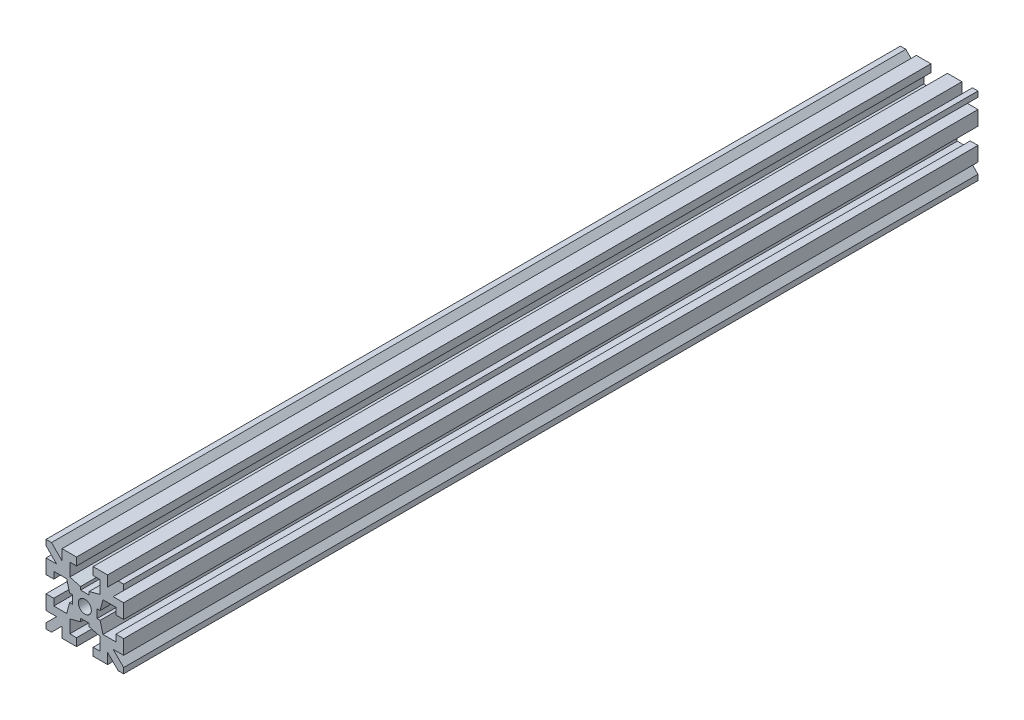
SolidWorks part; units mm, degrees
material "3.0205 (EN-AW 1200)"
ref_plane "Plano frontal" through (0, 0, 0) normal (0, 0, 1) x (1, 0, 0)
ref_plane "Plano superior" through (0, 0, 0) normal (0, 1, 0) x (1, 0, 0)
ref_plane "Plano direito" through (0, 0, 0) normal (1, 0, 0) x (0, 0, -1)
sketch "Esboço1" plane through (0, 0, 0) normal (0, 0, 1) x (1, 0, 0)
  line L0 (-25.7554, 0) -> (0, 0) construction
  line L1 (0, 0) -> (0, 21.5914) construction
  line L2 (0, 2.35) -> (-0.825, 2.35)
  line L3 (-0.825, 2.35) -> (-0.825, 2.95)
  line L4 (-0.825, 2.95) -> (-2.9, 3.5)
  line L5 (-2.9, 3.5) -> (-2.9, 6)
  line L6 (-2.9, 6) -> (-1.6, 6)
  line L7 (-1.6, 6) -> (-1.6, 7.5)
  line L8 (-1.6, 7.5) -> (-4.4, 7.5)
  line L9 (-4.4, 7.5) -> (-4.4, 5.4607)
  line L10 (-4.4, 5.4607) -> (-6.4393, 7.5)
  line L11 (-6.4393, 7.5) -> (-7.5, 7.5)
  line L12 (-7.5, 7.5) -> (0, 0) construction
  line L13 (-2.35, 0) -> (-2.35, 0.825)
  line L14 (-7.5, 6.4393) -> (-7.5, 7.5)
  line L15 (-5.4607, 4.4) -> (-7.5, 6.4393)
  line L16 (-7.5, 4.4) -> (-5.4607, 4.4)
  line L17 (-7.5, 1.6) -> (-7.5, 4.4)
  line L18 (-6, 1.6) -> (-7.5, 1.6)
  line L19 (-6, 2.9) -> (-6, 1.6)
  line L20 (-3.5, 2.9) -> (-6, 2.9)
  line L21 (-2.95, 0.825) -> (-3.5, 2.9)
  line L22 (-2.35, 0.825) -> (-2.95, 0.825)
  line L23 (-2.35, 0) -> (0, 0)
  line L24 (0, 0) -> (0, 2.35)
  dimension "D1" = 45
  dimension "D2" = 4.7
  dimension "D3" = 5.8
  dimension "D4" = 15
  dimension "D5" = 3.1
  dimension "D6" = 3.2
  dimension "D7" = 0.6
  dimension "D8" = 1.65
  dimension "D9" = 1.5
  dimension "D10" = 2.5
  dimension "D11" = 1.5
extrude "Ressalto-extrusão1" add sketch "Esboço1" along normal mid plane 165
mirror "Espelhar1" about plane through (0, 0, 0) normal (0, 1, 0) of "Ressalto-extrusão1"
mirror "Espelhar2" about plane through (0, 0, 0) normal (1, 0, 0) of "Espelhar1", "Ressalto-extrusão1"
sketch "Esboço2" plane through (0, 0, 82.5) normal (0, 0, 1) x (1, 0, 0)
  circle A0 centre (0, 0) radius 1.25
  dimension "D1" = 2.5
extrude "Corte-extrusão1" cut sketch "Esboço2" against normal through all both and the other way through all
